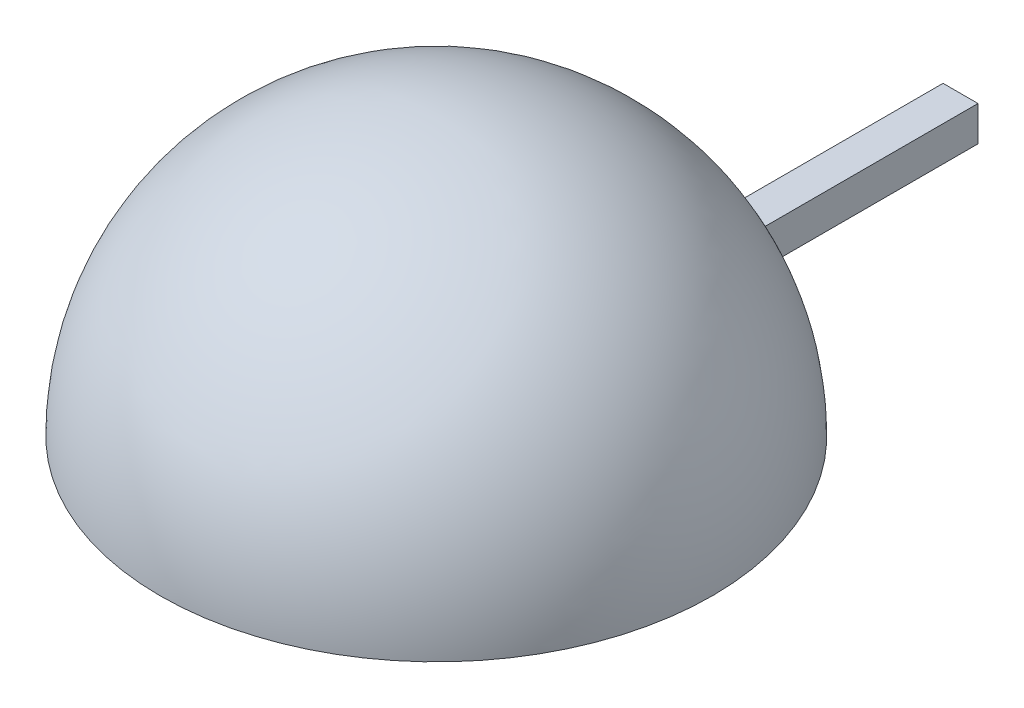
SolidWorks part; units mm, degrees
ref_plane "Спереди" through (0, 0, 0) normal (0, 0, 1) x (1, 0, 0)
ref_plane "Сверху" through (0, 0, 0) normal (0, 1, 0) x (1, 0, 0)
ref_plane "Справа" through (0, 0, 0) normal (1, 0, 0) x (0, 0, -1)
sketch "Эскиз1" plane through (0, 0, 0) normal (0, 1, 0) x (1, 0, 0)
  line L0 (0, 0) -> (0, 16.3344) construction
  line L2 (1, 0) -> (-1, 0)
  line L3 (1, 0) -> (1, 15)
  line L4 (1, 15) -> (-1, 15)
  line L5 (-1, 0) -> (-1, 15)
  point P7 (0, 0)
  dimension "D1" = 2
  dimension "D2" = 15
extrude "Бобышка-Вытянуть1" add sketch "Эскиз1" along normal blind 2
sketch "Эскиз2" plane through (0, 0, 0) normal (0, 1, 0) x (1, 0, 0)
  line L0 (0, 0) -> (0, -15) construction
  line L1 (0, -15) -> (0, -21.0949) construction
  line L2 (0, 0.8) -> (0, 0)
  line L3 (0, -30) -> (0, -30.8)
  arc A0 (0, 0) -> (0, -30) centre (0, -15) ccw
  arc A1 (0, 0.8) -> (0, -30.8) centre (0, -15) ccw
  dimension "D1" = 15
  dimension "D2" = 0.8
revolve "Повернуть1" add sketch "Эскиз2" angle 180 about L1
equation "\"толщина ножки\"= 2мм"
equation "\"D1@Бобышка-Вытянуть1\"=\"толщина ножки\""
equation "\"D1@Эскиз1\"= \"толщина ножки\""
equation "\"D2@Эскиз1\" = \"длина ножки\""
equation "\"радиус чашки\"= 15мм"
equation "\"D1@Эскиз2\"=\"радиус чашки\""
equation "\"толщина чашки\"= 0.8мм"
equation "\"D2@Эскиз2\"=\"толщина чашки\""
equation "\"длина ножки\"= 15мм"
